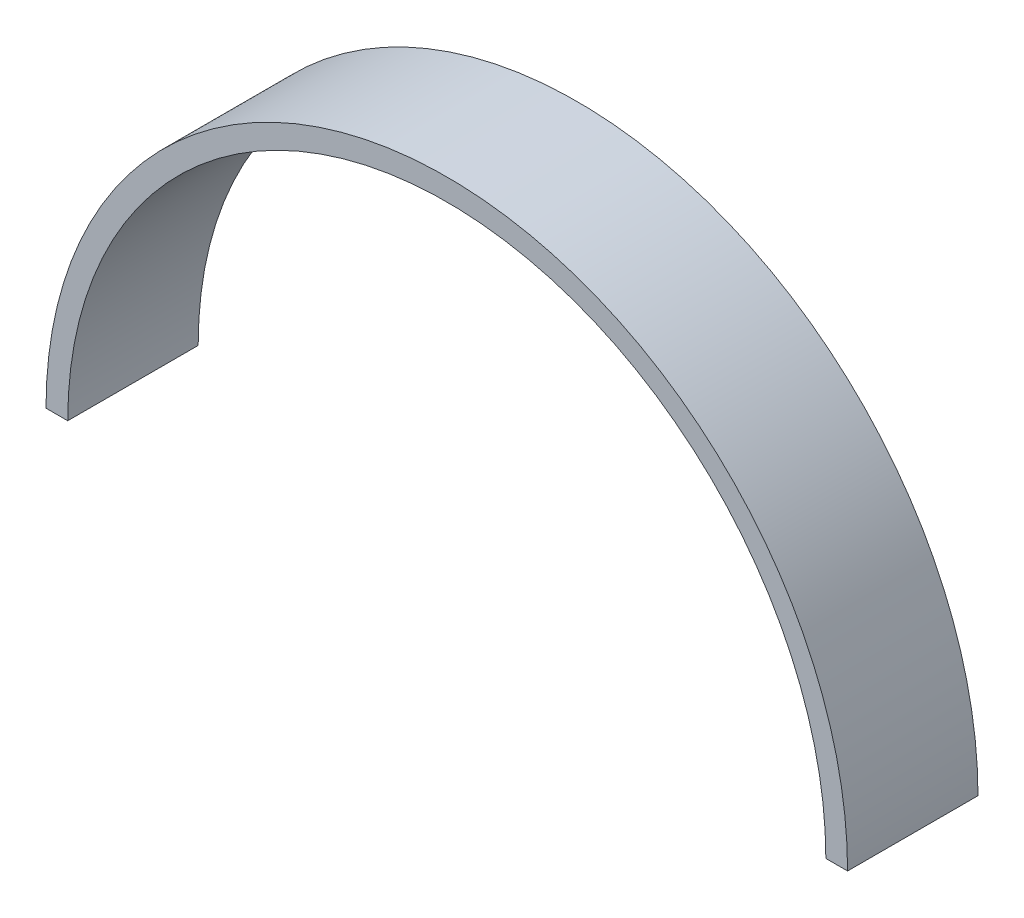
SolidWorks part; units mm, degrees
material "Natural Rubber"
ref_plane "Front Plane" through (0, 0, 0) normal (0, 0, 1) x (1, 0, 0)
ref_plane "Top Plane" through (0, 0, 0) normal (0, 1, 0) x (1, 0, 0)
ref_plane "Right Plane" through (0, 0, 0) normal (1, 0, 0) x (0, 0, -1)
sketch "Sketch1" plane through (0, 0, 0) normal (0, 0, 1) x (1, 0, 0)
  line L0 (-58.545, 0) -> (-55.37, 0)
  line L1 (55.37, 0) -> (58.545, 0)
  arc A0 (-58.545, 0) -> (58.545, 0) centre (0, 0) cw
  arc A1 (-55.37, 0) -> (55.37, 0) centre (0, 0) cw
  dimension "D1" = 58.545
  dimension "D2" = 3.175
extrude "Boss-Extrude1" add sketch "Sketch1" along normal blind 19.05
